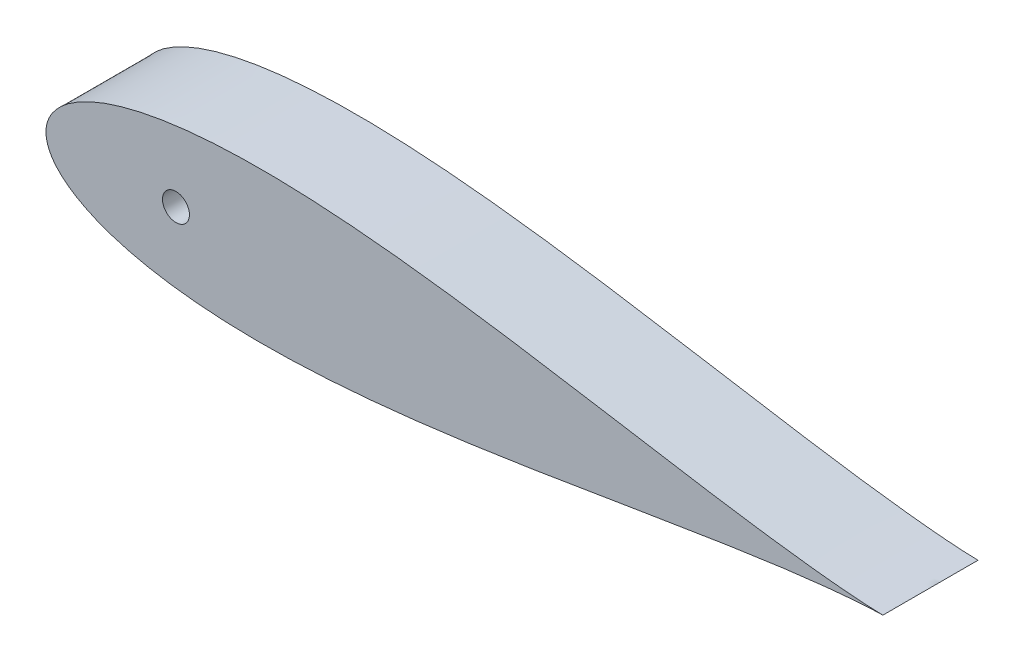
SolidWorks part; units mm, degrees
ref_plane "Front Plane" through (0, 0, 0) normal (0, 0, 1) x (1, 0, 0)
ref_plane "Top Plane" through (0, 0, 0) normal (0, 1, 0) x (1, 0, 0)
ref_plane "Right Plane" through (0, 0, 0) normal (1, 0, 0) x (0, 0, -1)
sketch "Sketch1" plane through (0, 0, 0) normal (0, 0, 1) x (1, 0, 0)
  line L0 (100, 0) -> (0, 0) construction
  line L1 (1.2169, -991.9959) -> (1.2169, 49008.0041) construction
  line L2 (93.345, 0) -> (114.935, 0) construction
  line L3 (125.634, 0) -> (131.6629, 0) construction
  line L4 (643.5991, 0) -> (643.5991, -1.016)
  line L9 (0, 0) -> (643.9668, 0)
  line L13 (460.661, 0) -> (473.361, 0)
  circle A0 centre (104.14, 0) radius 10.795 construction
  arc A1 (1.2169, -4.6585) -> (1.2169, 4.6585) centre (9.525, 0) cw
  arc A2 (641.5671, 0) -> (644.1071, 0) centre (642.8371, 0) ccw
  circle A4 centre (104.14, 0) radius 10.795
  circle A9 centre (40.64, 0) radius 12.7
  circle A14 centre (642.3793, 0) radius 1.5875 construction
  arc A15 (642.5108, -1.582) -> (642.5108, 1.582) centre (642.3793, 0) ccw
  spline S2 degree 3 poles (666.3448, -0.0547) (672.2538, 0) (666.3448, 0.0547) (662.8509, 0.2344) (656.505, 0.5436) (649.293, 1.0348) (640.4916, 1.7319) (630.4138, 2.6634) (619.0141, 3.8493) (606.375, 5.3044) (592.5439, 7.0376) (577.5855, 9.0506) (561.5643, 11.3389) (544.5497, 13.8907) (526.6141, 16.6877) (507.8326, 19.7051) (488.2827, 22.9117) (468.0444, 26.2704) (447.1994, 29.739) (425.8316, 33.2703) (404.0263, 36.8132) (381.8707, 40.3133) (359.4533, 43.7135) (336.8645, 46.9554) (314.1962, 49.9798) (291.5418, 52.7277) (268.9963, 55.1412) (246.6566, 57.1646) (224.6209, 58.7452) (202.9892, 59.8341) (181.8631, 60.3875) (161.3458, 60.367) (141.542, 59.7399) (122.5581, 58.4818) (104.5023, 56.5743) (87.485, 54.0089) (71.6197, 50.7848) (57.0237, 46.9125) (43.8205, 42.415) (32.1416, 37.3322) (22.1291, 31.7315) (13.9324, 25.7264) (7.6896, 19.5132) (3.4631, 13.4204) (1.1063, 7.9234) (0.1546, 3.5138) (-0.0622, 0) (0.1546, -3.5138) (1.1063, -7.9234) (3.4631, -13.4204) (7.6896, -19.5132) (13.9324, -25.7264) (22.1291, -31.7315) (32.1416, -37.3322) (43.8205, -42.415) (57.0237, -46.9125) (71.6197, -50.7848) (87.485, -54.0089) (104.5023, -56.5743) (122.5581, -58.4818) (141.542, -59.7399) (161.3458, -60.367) (181.8631, -60.3875) (202.9892, -59.8341) (224.6209, -58.7452) (246.6566, -57.1646) (268.9963, -55.1412) (291.5418, -52.7277) (314.1962, -49.9798) (336.8645, -46.9554) (359.4533, -43.7135) (381.8707, -40.3133) (404.0263, -36.8132) (425.8316, -33.2703) (447.1994, -29.739) (468.0444, -26.2704) (488.2827, -22.9117) (507.8326, -19.7051) (526.6141, -16.6877) (544.5497, -13.8907) (561.5643, -11.3389) (577.5855, -9.0506) (592.5439, -7.0376) (606.375, -5.3044) (619.0141, -3.8493) (630.4138, -2.6634) (640.4916, -1.7319) (649.293, -1.0348) (656.505, -0.5436) (662.8509, -0.2344) (666.3448, -0.0547) (672.2538, 0) (666.3448, 0.0547) knots -0.009667 -0.005395 -0.002168 0 0.002168 0.005395 0.009667 0.014967 0.021271 0.028553 0.036781 0.04592 0.055932 0.066773 0.078397 0.090755 0.103793 0.117456 0.131686 0.146422 0.1616 0.177156 0.193024 0.209135 0.225421 0.241812 0.258238 0.274629 0.290914 0.307025 0.322893 0.338448 0.353626 0.368361 0.38259 0.396253 0.40929 0.421647 0.43327 0.444109 0.454119 0.463255 0.471479 0.478755 0.485052 0.490344 0.49461 0.497833 0.5 0.502167 0.50539 0.509656 0.514948 0.521245 0.528521 0.536745 0.545881 0.555891 0.56673 0.578353 0.59071 0.603747 0.61741 0.631639 0.646374 0.661552 0.677107 0.692975 0.709086 0.725371 0.741762 0.758188 0.774579 0.790865 0.806976 0.822844 0.8384 0.853578 0.868314 0.882544 0.896207 0.909245 0.921603 0.933227 0.944068 0.95408 0.963219 0.971447 0.978729 0.985033 0.990333 0.994605 0.997832 1 1.002168 1.005395 1.009667 only from (670.56, 0) to (670.56, 0)
  point P2 (167.64, 0)
  point P8 (1.2169, -4.6585)
  point P10 (1.2169, 4.6585)
  point P28 (133.9182, 0)
  point P49 (130.0977, 0)
  point P59 (95.1064, 0)
  dimension "D2" = 21.59
  dimension "D3" = 1.016
  dimension "D4" = 1.27
  dimension "D8" = 25.4
  dimension "D9" = 63.5
  dimension "D10" = 3.175
  dimension "D6" = 63.5
extrude "Boss-Extrude1" add sketch "Sketch1" along normal blind 76.2 contours S2
sketch "Sketch3" plane through (0, 0, 76.2) normal (0, 0, 1) x (1, 0, 0)
  circle A0 centre (104.1392, 0) radius 10.795
  dimension "D1" = 21.59
extrude "Cut-Extrude2" cut sketch "Sketch3" against normal blind 76.2
